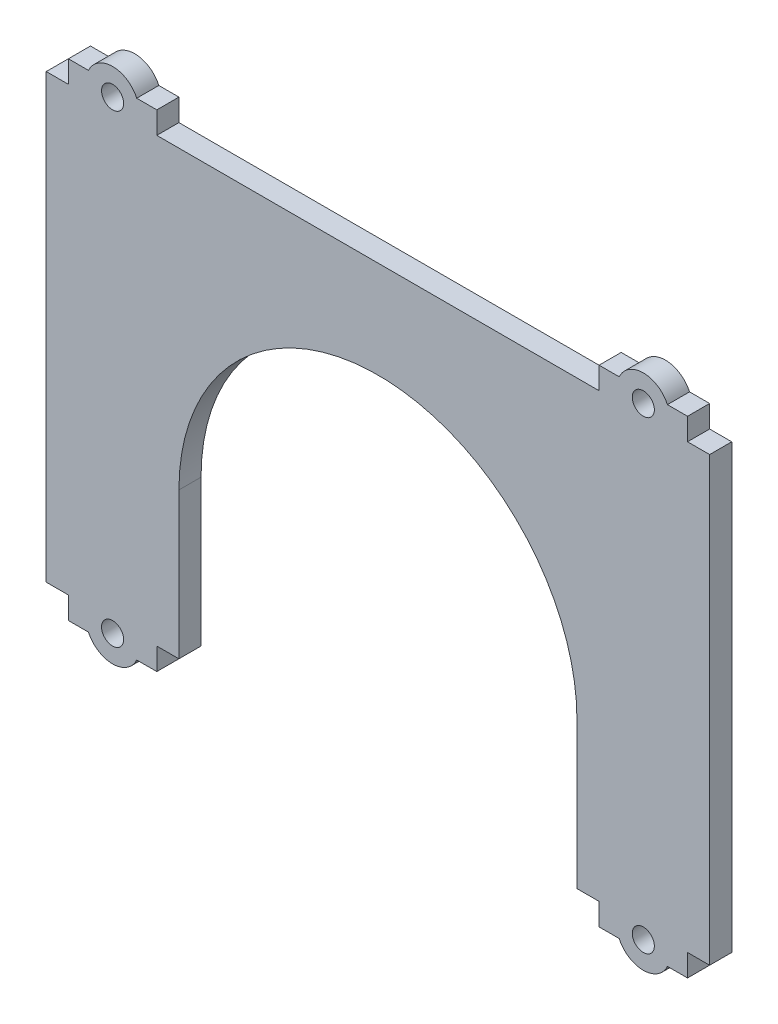
SolidWorks part; units mm, degrees
ref_plane "Front Plane" through (0, 0, 0) normal (0, 0, 1) x (1, 0, 0)
ref_plane "Top Plane" through (0, 0, 0) normal (0, 1, 0) x (1, 0, 0)
ref_plane "Right Plane" through (0, 0, 0) normal (1, 0, 0) x (0, 0, -1)
sketch "Sketch1" plane through (0, 0, 0) normal (0, 0, 1) x (1, 0, 0)
  line L1 (75, 50) -> (-75, 50)
  line L2 (75, 50) -> (75, -50)
  line L3 (75, -50) -> (-75, -50)
  line L4 (-75, 50) -> (-75, -50)
  line L5 (75, 50) -> (-75, -50) construction
  line L6 (75, -50) -> (-75, 50) construction
  point P0 (0, 0)
  dimension "D1" = 150
  dimension "D2" = 100
extrude "Boss-Extrude1" add sketch "Sketch1" along normal blind 5
sketch "Sketch3" plane through (0, -50, 0) normal (0, -1, 0) x (1, 0, 0)
  line L0 (-75, 0) -> (75, 0) construction
  line L1 (-70, 0) -> (-50, 0)
  line L2 (-70, 0) -> (-70, 5)
  line L3 (-70, 5) -> (-50, 5)
  line L4 (-50, 0) -> (-50, 5)
  line L5 (-75, 5) -> (75, 5) construction
  line L6 (-75, 5) -> (-75, 0) construction
  point P8 (-70, 2.5)
  dimension "D1" = 5
  dimension "D2" = 5
  dimension "D3" = 20
extrude "Boss-Extrude2" add sketch "Sketch3" along normal blind 5
mirror "Mirror1" about plane through (0, 0, 0) normal (1, 0, 0) of "Boss-Extrude2" second plane through (0, 0, 0) second plane normal (0, 1, 0)
sketch "Sketch4" plane through (0, 0, 5) normal (0, 0, 1) x (1, 0, 0)
  line L0 (70, 55) -> (70, 50) construction
  line L1 (50, 50) -> (-50, 50) construction
  line L2 (50, 55) -> (70, 55) construction
  circle A0 centre (60, 52.5) radius 6
  dimension "D1" = 12
  dimension "D2" = 10
  dimension "D3" = 2.5
  dimension "2.5" = 2.5
extrude "Boss-Extrude3" add sketch "Sketch4" against normal blind 5
sketch "Sketch5" plane through (0, 0, 5) normal (0, 0, 1) x (1, 0, 0)
  line L0 (50, 55) -> (54.5456, 55) construction
  line L1 (50, 55) -> (50, 50) construction
  circle A0 centre (60, 52.5) radius 2.5
  arc A1 (65.4544, 55) -> (54.5456, 55) centre (60, 52.5) ccw construction
  dimension "D1" = 5
  dimension "D2" = 2.5
  dimension "D3" = 5
  dimension "D4" = 10
  dimension "D5" = 3.5
extrude "Cut-Extrude1" cut sketch "Sketch5" against normal blind 5
mirror "Mirror2" about plane through (0, 0, 0) normal (1, 0, 0) of "Boss-Extrude3", "Cut-Extrude1" second plane through (0, 0, 0) second plane normal (0, 1, 0)
sketch "Sketch8" plane through (0, 0, 5) normal (0, 0, 1) x (1, 0, 0)
  line L0 (-45, -16.928) -> (-45, -50)
  line L1 (-50, -50) -> (50, -50) construction
  line L2 (45, -16.928) -> (45, -50)
  line L3 (75, -50) -> (75, 50) construction
  line L4 (-75, 50) -> (-75, -50) construction
  line L5 (50, 50) -> (-50, 50) construction
  arc A0 (45, -16.928) -> (-45, -16.928) centre (0, -16.928) ccw
  dimension "D1" = 90
  dimension "D2" = 45
  dimension "D5" = 33.072
  dimension "D6" = 45
  dimension "D7" = 66.928
  dimension "D3" = 30
  dimension "D4" = 30
extrude "Cut-Extrude3" cut sketch "Sketch8" against normal blind 5 and the other way through all flip side to cut
